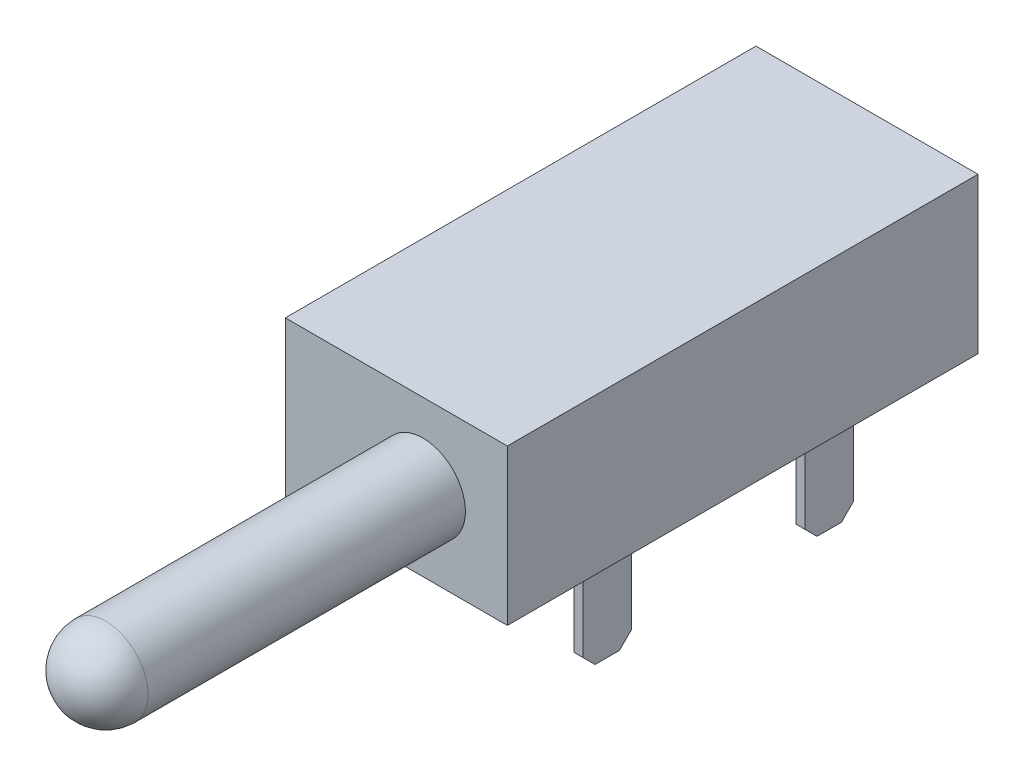
SolidWorks part; units mm, degrees
ref_plane "Front" through (0, 0, 0) normal (0, 0, 1) x (1, 0, 0)
ref_plane "Top" through (0, 0, 0) normal (0, 1, 0) x (1, 0, 0)
ref_plane "Right" through (0, 0, 0) normal (1, 0, 0) x (0, 0, -1)
sketch "Sketch1" plane through (0, 0, 0) normal (0, 0, 1) x (1, 0, 0)
  line L1 (-7.874, -4.445) -> (4.826, -4.445)
  line L2 (-7.874, -4.445) -> (-7.874, 4.445)
  line L3 (-7.874, 4.445) -> (4.826, 4.445)
  line L4 (4.826, -4.445) -> (4.826, 4.445)
  line L5 (-1.524, 4.445) -> (-1.524, -4.445) construction
  line L6 (-7.874, 0) -> (4.826, 0) construction
  point P0 (-1.524, 0)
  dimension "D1" = 8.89
  dimension "D2" = 12.7
  dimension "D3" = 7.874
extrude "Boss-Extrude1" add sketch "Sketch1" against normal blind 26.924 contours L3 L4 L1 L2
sketch "Sketch2" plane through (0, 0, 0) normal (0, 0, 1) x (1, 0, 0)
  circle A0 centre (0, 0) radius 2.4257
  dimension "D1" = 4.8514
extrude "Boss-Extrude2" add sketch "Sketch2" along normal blind 20.574
fillet "Fillet1" radius 2.4257 1 edges at (2.4257, 0, 20.574)
sketch "Sketch3" plane through (0, -4.445, 0) normal (0, -1, 0) x (1, 0, 0)
  line L0 (-1.524, 0) -> (-1.524, -26.924) construction
  line L1 (-7.874, 0) -> (4.826, 0) construction
  line L2 (-7.874, -26.924) -> (4.826, -26.924) construction
  line L3 (4.826, -13.462) -> (-7.874, -13.462) construction
  line L4 (4.826, -26.924) -> (4.826, 0) construction
  line L5 (-7.874, -26.924) -> (-7.874, 0) construction
  line L7 (-4.699, -14.859) -> (-5.207, -14.859)
  line L8 (-4.699, -14.859) -> (-4.699, -12.065)
  line L9 (-4.699, -12.065) -> (-5.207, -12.065)
  line L10 (-5.207, -14.859) -> (-5.207, -12.065)
  line L11 (-4.953, -12.065) -> (-4.953, -14.859) construction
  line L12 (-4.699, -13.462) -> (-5.207, -13.462) construction
  line L13 (1.651, -19.685) -> (2.159, -19.685)
  line L14 (1.651, -19.685) -> (1.651, -22.479)
  line L15 (1.651, -22.479) -> (2.159, -22.479)
  line L16 (2.159, -19.685) -> (2.159, -22.479)
  line L17 (1.905, -22.479) -> (1.905, -19.685) construction
  line L18 (1.651, -21.082) -> (2.159, -21.082) construction
  line L19 (2.159, -9.779) -> (1.651, -9.779)
  line L20 (2.159, -9.779) -> (2.159, -6.985)
  line L21 (2.159, -6.985) -> (1.651, -6.985)
  line L22 (1.651, -9.779) -> (1.651, -6.985)
  line L23 (1.905, -6.985) -> (1.905, -9.779) construction
  line L24 (2.159, -8.382) -> (1.651, -8.382) construction
  point P12 (-4.953, -13.462)
  point P16 (1.905, -21.082)
  point P23 (1.905, -8.382)
  dimension "D1" = 2.794
  dimension "D2" = 0.508
  dimension "D3" = 3.429
  dimension "D4" = 2.794
  dimension "D5" = 0.508
  dimension "D6" = 2.794
  dimension "D7" = 0.508
  dimension "D8" = 7.62
  dimension "D9" = 5.08
  dimension "D10" = 3.429
extrude "Boss-Extrude3" add sketch "Sketch3" along normal blind 7.112
chamfer "Chamfer1" distance 0.6985 angle 45 6 edges at (1.905, -11.557, -6.985) (1.905, -11.557, -9.779) (1.905, -11.557, -22.479) (1.905, -11.557, -19.685) (-4.953, -11.557, -14.859) (-4.953, -11.557, -12.065)
